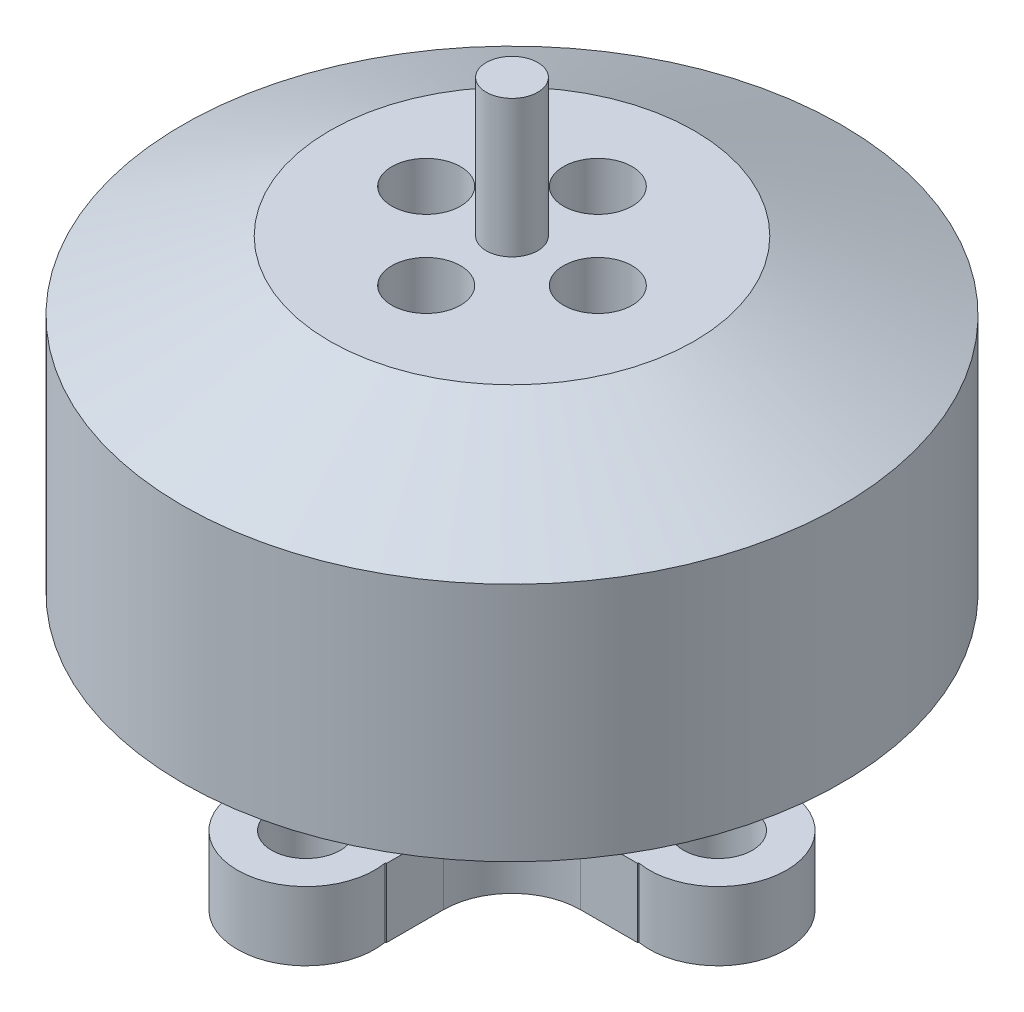
SolidWorks part; units mm, degrees
ref_plane "Front Plane" through (0, 0, 0) normal (0, 0, 1) x (1, 0, 0)
ref_plane "Top Plane" through (0, 0, 0) normal (0, 1, 0) x (1, 0, 0)
ref_plane "Right Plane" through (0, 0, 0) normal (1, 0, 0) x (0, 0, -1)
sketch "Sketch1" plane through (0, 0, 0) normal (0, 1, 0) x (1, 0, 0)
  line L1 (-2, 6) -> (2, 6)
  line L2 (-2, 6) -> (-2, -6)
  line L3 (-2, -6) -> (2, -6)
  line L4 (2, 6) -> (2, -6)
  line L5 (-6, 2) -> (6, 2)
  line L6 (-6, 2) -> (-6, -2)
  line L7 (-6, -2) -> (6, -2)
  line L8 (6, 2) -> (6, -2)
  circle A0 centre (0, 0) radius 6
  circle A1 centre (0, 6) radius 1
  circle A2 centre (0, -6) radius 1
  circle A3 centre (6, 0) radius 1
  circle A4 centre (-6, 0) radius 1
  circle A5 centre (0, 0) radius 8
  circle A6 centre (0, 6) radius 2
  circle A7 centre (6, 0) radius 2
  circle A8 centre (0, -6) radius 2
  circle A9 centre (-6, 0) radius 2
  circle A10 centre (0, 0) radius 2
  dimension "D1" = 12
  dimension "D2" = 2
  dimension "D3" = 16
extrude "Boss-Extrude1" add sketch "Sketch1" along normal blind 2 contours A8 A0 L4 L7 L2 | A7 A0 L5 L4 L7 | A6 A0 L2 L5 L4 | A9 A0 L7 L2 L5 | A10 L5 L2 | A10 L4 L5 | A10 L7 L4 | A10 L2 L7 | A3 | A1 | A4 | A2
fillet "Fillet1" radius 2 4 edges at (-2, 1, 2) (-2, 1, -2) (2, 1, -2) (2, 1, 2)
sketch "Sketch2" plane through (0, 2, 0) normal (0, 1, 0) x (1, 0, 0)
  circle A0 centre (0, 0) radius 3
  dimension "D1" = 6
extrude "Boss-Extrude2" add sketch "Sketch2" along normal blind 3
sketch "Sketch3" plane through (0, 5, 0) normal (0, 1, 0) x (1, 0, 0)
  circle A0 centre (0, 0) radius 9.6
  dimension "D1" = 19.2
extrude "Boss-Extrude3" add sketch "Sketch3" along normal offset from surface (9 mm away) 14 up to face at (0, 0, 0)
sketch "Sketch4" plane through (0, 14, 0) normal (0, 1, 0) x (1, 0, 0)
  circle A0 centre (0, 0) radius 0.75
  dimension "D1" = 1.5
extrude "Boss-Extrude4" add sketch "Sketch4" along normal blind 4
sketch "Sketch5" plane through (0, 14, 0) normal (0, 1, 0) x (1, 0, 0)
  circle A0 centre (0, 0) radius 2.5
  circle A1 centre (-2.5, 0) radius 1
  circle A2 centre (0, 2.5) radius 1
  circle A3 centre (2.5, 0) radius 1
  circle A4 centre (0, -2.5) radius 1
  dimension "D1" = 5
  dimension "D2" = 2
extrude "Cut-Extrude1" cut sketch "Sketch5" against normal blind 4 contours A2 | A3 | A4 | A1
chamfer "Chamfer1" distance 2 angle 65 1 edges at (0, 14, 9.6)
sketch "Sketch6" plane through (0, 5, 0) normal (0, -1, 0) x (1, 0, 0)
  circle A0 centre (0, 0) radius 8.1
  circle A1 centre (0, 0) radius 7.6
  circle A2 centre (0, 0) radius 9.6 construction
  dimension "D1" = 1.5
  dimension "D2" = 0.5
extrude "Cut-Extrude2" cut sketch "Sketch6" against normal offset from surface (6.0444 mm away) 1.5
